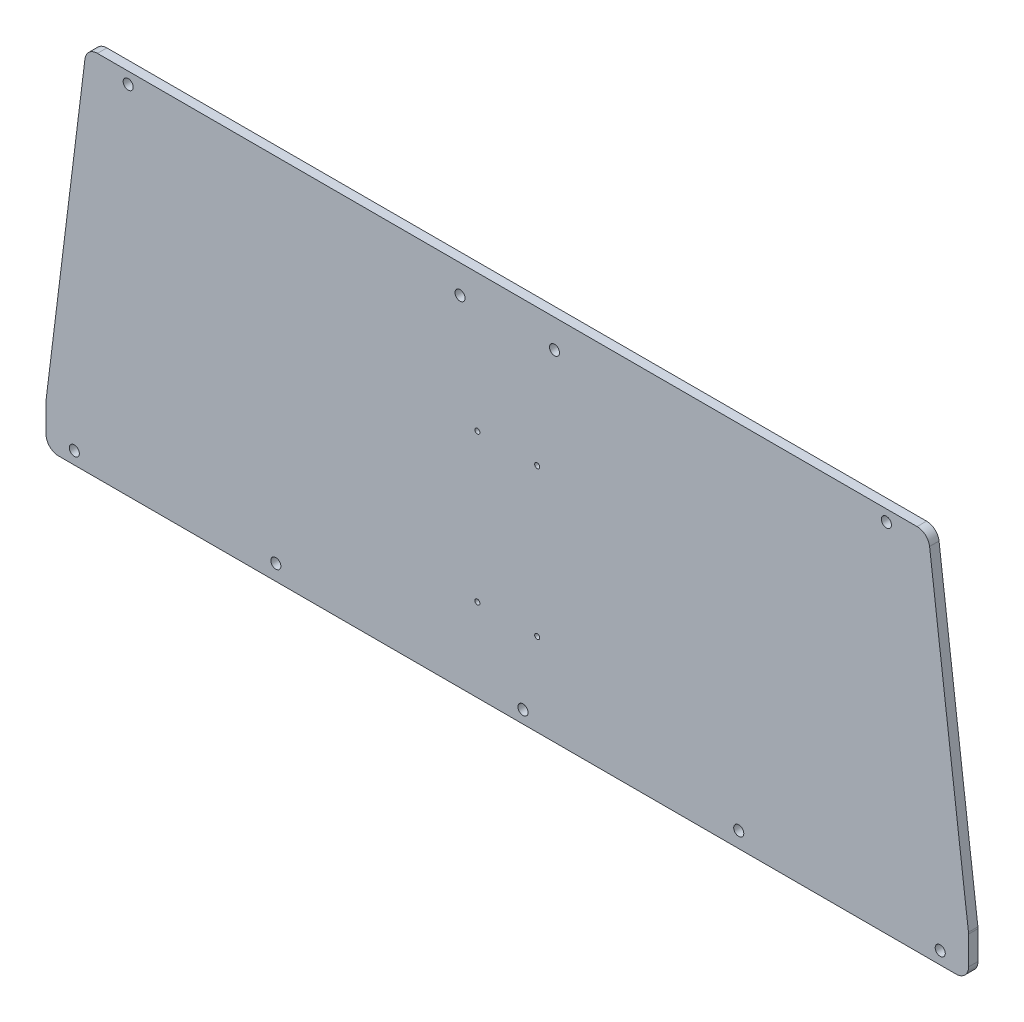
SolidWorks part; units mm, degrees
ref_plane "Front Plane" through (0, 0, 0) normal (0, 0, 1) x (1, 0, 0)
ref_plane "Top Plane" through (0, 0, 0) normal (0, 1, 0) x (1, 0, 0)
ref_plane "Right Plane" through (0, 0, 0) normal (1, 0, 0) x (0, 0, -1)
ref_plane "Plane1" through (0, -0.9245, 8.3996) normal (0, 0.1094, -0.994) x (-1, 0, 0)
sketch "Sketch1" plane through (0, 0, 0) normal (0, 0, 1) x (1, 0, 0)
  line L0 (-11.619, 112.409) -> (11.619, 112.409)
  line L11 (-146.5568, 8.4625) -> (-146.5568, -0.5793)
  line L12 (-134.178, 108.9176) -> (-146.527, 8.947)
  line L13 (-11.619, 112.409) -> (-130.2079, 112.409)
  line L14 (130.2079, 112.409) -> (11.619, 112.409)
  line L15 (146.527, 8.947) -> (134.178, 108.9176)
  line L16 (146.5568, -0.5793) -> (146.5568, 8.4625)
  line L17 (-142.5568, -4.5552) -> (142.5568, -4.5552)
  line L18 (-146.5568, 8.4625) -> (-146.5568, -0.5793)
  line L19 (-134.178, 108.9176) -> (-146.527, 8.947)
  line L20 (-11.619, 112.409) -> (-130.2079, 112.409)
  line L21 (130.2079, 112.409) -> (11.619, 112.409)
  line L22 (146.527, 8.947) -> (134.178, 108.9176)
  line L23 (146.5568, -0.5793) -> (146.5568, 8.4625)
  line L24 (-142.5568, -4.5552) -> (142.5568, -4.5552)
  ellipse E9 centre (-142.5568, 8.4625) end of major axis (-138.5568, 8.4625) minor radius 3.976 (-146.527, 8.947) -> (-146.5568, 8.4625) ccw
  ellipse E10 centre (-130.2079, 108.433) end of major axis (-126.2079, 108.433) minor radius 3.976 (-130.2079, 112.409) -> (-134.178, 108.9176) ccw
  ellipse E11 centre (-11.619, 106.445) end of major axis (-17.619, 106.445) minor radius 5.964 (-5.8095, 107.936) -> (-11.619, 112.409) ccw
  ellipse E12 centre (0, 109.427) end of major axis (6, 109.427) minor radius 5.964 (-5.8095, 107.936) -> (5.8095, 107.936) ccw
  ellipse E13 centre (11.619, 106.445) end of major axis (5.619, 106.445) minor radius 5.964 (11.619, 112.409) -> (5.8095, 107.936) ccw
  ellipse E14 centre (130.2079, 108.433) end of major axis (134.2079, 108.433) minor radius 3.976 (134.178, 108.9176) -> (130.2079, 112.409) ccw
  ellipse E15 centre (142.5568, 8.4625) end of major axis (146.5568, 8.4625) minor radius 3.976 (146.5568, 8.4625) -> (146.527, 8.947) ccw
  ellipse E16 centre (142.5568, -0.5793) end of major axis (146.5568, -0.5793) minor radius 3.976 (142.5568, -4.5552) -> (146.5568, -0.5793) ccw
  ellipse E17 centre (-142.5568, -0.5793) end of major axis (-138.5568, -0.5793) minor radius 3.976 (-146.5568, -0.5793) -> (-142.5568, -4.5552) ccw
  ellipse E18 centre (-142.5568, 8.4625) end of major axis (-138.5568, 8.4625) minor radius 3.976 (-146.527, 8.947) -> (-146.5568, 8.4625) ccw
  ellipse E19 centre (-130.2079, 108.433) end of major axis (-126.2079, 108.433) minor radius 3.976 (-130.2079, 112.409) -> (-134.178, 108.9176) ccw
  ellipse E23 centre (130.2079, 108.433) end of major axis (134.2079, 108.433) minor radius 3.976 (134.178, 108.9176) -> (130.2079, 112.409) ccw
  ellipse E24 centre (142.5568, 8.4625) end of major axis (146.5568, 8.4625) minor radius 3.976 (146.5568, 8.4625) -> (146.527, 8.947) ccw
  ellipse E25 centre (142.5568, -0.5793) end of major axis (146.5568, -0.5793) minor radius 3.976 (142.5568, -4.5552) -> (146.5568, -0.5793) ccw
  ellipse E26 centre (-142.5568, -0.5793) end of major axis (-138.5568, -0.5793) minor radius 3.976 (-146.5568, -0.5793) -> (-142.5568, -4.5552) ccw
  dimension "D1" = 0
extrude "Boss-Extrude1" add sketch "Sketch1" against normal blind 3
hole_wizard "Ø3.2 (3.2) Diameter Hole1" positions "Sketch4" profile "Sketch3" hole size "Ø3.2" standard "ANSI Metric"
sketch "Sketch4" plane through (167.5193, 69.7099, 0) normal (0, 0, 1) x (1, 0, 0)
  point P32 (-47.0706, 39.0624)
  point P35 (-29.9625, -70.2891)
  point P38 (-93.9811, -69.2951)
  point P41 (-241.0575, -69.2951)
  point P44 (-305.0762, -70.2891)
  point P47 (-287.968, 39.0624)
  point P50 (-182.5193, 33.6991)
  point P53 (-152.5193, 33.6991)
  point P56 (-162.5193, -70.2891)
sketch "Sketch3" plane through (120.4487, 108.7723, 0) normal (1, 0, 0) x (0, -1, 0)
  line L0 (0, 0) -> (0, 15.9614)
  line L1 (0, 15.9614) -> (1.6, 15)
  line L2 (1.6, 15) -> (1.6, 0)
  line L5 (1.6, 0) -> (0, 0)
  line L10 (0, 15.9614) -> (-1.6, 15) construction
  line L11 (0, -6.35) -> (0, 107.95) construction
  dimension "Hole Dia." = 3.2
  dimension "Hole Depth" = 15
  dimension "Drill Angle" = 118
hole_wizard "Ø1.6 (1.6) Diameter Hole1" positions "Sketch6" profile "Sketch5" hole size "Ø1.6" standard "ANSI Metric"
sketch "Sketch6" plane through (0, 0, 0) normal (0, 0, 1) x (1, 0, 0)
  point P0 (-9.5, 68.809)
  point P3 (9.5, 68.809)
  point P6 (-9.5, 21.809)
  point P9 (9.5, 21.809)
sketch "Sketch5" plane through (-9.5, 68.809, 0) normal (1, 0, 0) x (0, -1, 0)
  line L0 (0, 0) -> (0, 15.4807)
  line L1 (0, 15.4807) -> (0.8, 15)
  line L2 (0.8, 15) -> (0.8, 0)
  line L5 (0.8, 0) -> (0, 0)
  line L10 (0, 15.4807) -> (-0.8, 15) construction
  line L11 (0, -6.35) -> (0, 107.95) construction
  dimension "Hole Dia." = 1.6
  dimension "Hole Depth" = 15
  dimension "Drill Angle" = 118
